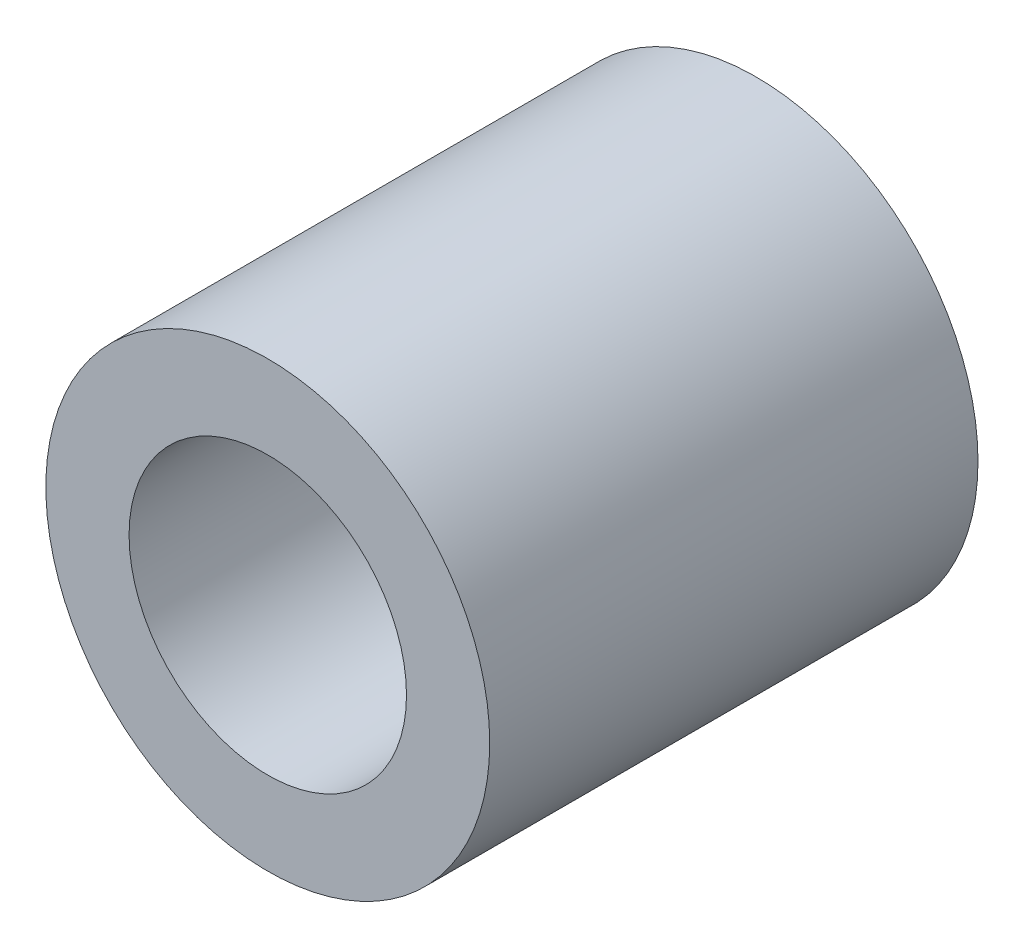
SolidWorks part; units mm, degrees
ref_plane "Front Plane" through (0, 0, 0) normal (0, 0, 1) x (1, 0, 0)
ref_plane "Top Plane" through (0, 0, 0) normal (0, 1, 0) x (1, 0, 0)
ref_plane "Right Plane" through (0, 0, 0) normal (1, 0, 0) x (0, 0, -1)
sketch "Sketch1" plane through (0, 0, 0) normal (0, 0, 1) x (1, 0, 0)
  circle A0 centre (-98.156, 22.86) radius 6.35
  circle A1 centre (-98.156, 22.86) radius 3.9688
  circle A2 centre (-98.156, 22.86) radius 4.191 construction
extrude "Boss-Extrude1" add sketch "Sketch1" along normal blind 13.97 contours A0 A1
